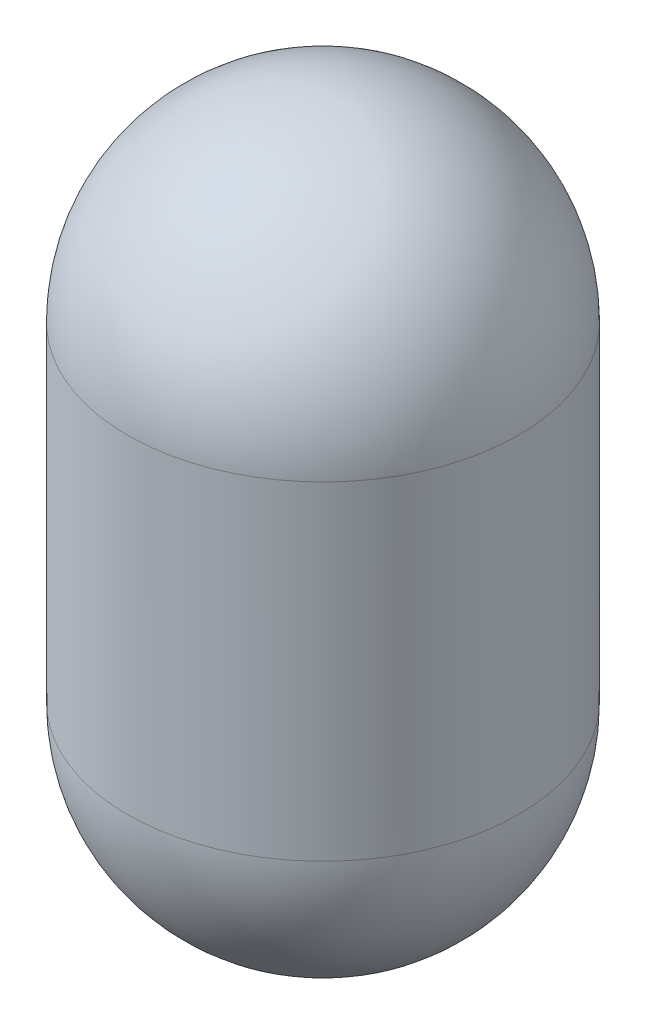
SolidWorks part; units mm, degrees
material "AISI 316 Annealed Stainless Steel Bar (SS)"
ref_plane "Front Plane" through (0, 0, 0) normal (0, 0, 1) x (1, 0, 0)
ref_plane "Top Plane" through (0, 0, 0) normal (0, 1, 0) x (1, 0, 0)
ref_plane "Right Plane" through (0, 0, 0) normal (1, 0, 0) x (0, 0, -1)
sketch "Sketch1" plane through (0, 0, 0) normal (0, 0, 1) x (1, 0, 0)
  line L0 (-158.75, -158.75) -> (-158.75, -425.45)
  line L1 (0, -425.45) -> (0, -158.75) construction
  line L2 (0, -584.2) -> (0, 0)
  arc A0 (0, 0) -> (-158.75, -158.75) centre (0, -158.75) ccw
  arc A1 (-158.75, -425.45) -> (0, -584.2) centre (0, -425.45) ccw
  dimension "D1" = 158.75
  dimension "D2" = 584.2
revolve "Revolve1" add sketch "Sketch1" angle 360 about L2
